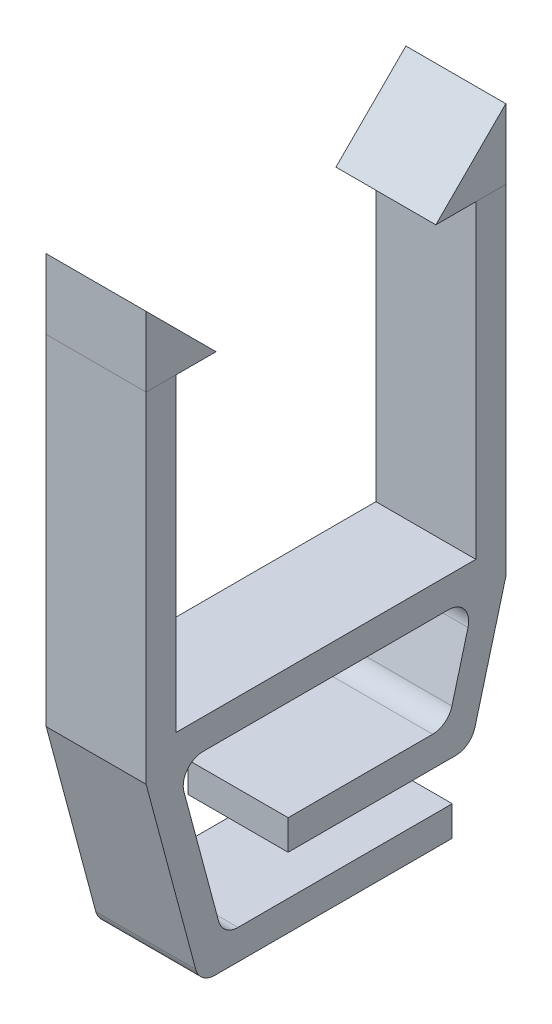
SolidWorks part; units mm, degrees
ref_plane "前视基准面" through (0, 0, 0) normal (0, 0, 1) x (1, 0, 0)
ref_plane "上视基准面" through (0, 0, 0) normal (0, 1, 0) x (1, 0, 0)
ref_plane "右视基准面" through (0, 0, 0) normal (1, 0, 0) x (0, 0, -1)
sketch "草图1" plane through (0, 0, 0) normal (0, 1, 0) x (1, 0, 0)
  line L1 (-10.9756, 9.0488) -> (-5.9756, 9.0488)
  line L2 (-10.9756, 9.0488) -> (-10.9756, -8.9512)
  line L3 (-10.9756, -8.9512) -> (-5.9756, -8.9512)
  line L4 (-5.9756, 9.0488) -> (-5.9756, -8.9512)
  line L5 (-10.9756, 7.5488) -> (-5.9756, 7.5488)
  line L6 (-10.9756, 7.5488) -> (-10.9756, -7.4512)
  line L7 (-10.9756, -7.4512) -> (-5.9756, -7.4512)
  line L8 (-5.9756, 7.5488) -> (-5.9756, -7.4512)
  dimension "D1" = 1.5
  dimension "D2" = 1.5
  dimension "D3" = 5
  dimension "D4" = 15
extrude "凸台-拉伸1" add sketch "草图1" along normal blind 15.5 contours L2 L5 L4 L1 | L7 L2 L3 L4
sketch "草图2" plane through (0, 0, 0) normal (0, -1, 0) x (1, 0, 0)
  line L1 (-5.9756, 8.9512) -> (-10.9756, 8.9512)
  line L2 (-5.9756, 8.9512) -> (-5.9756, -9.0488)
  line L3 (-5.9756, -9.0488) -> (-10.9756, -9.0488)
  line L4 (-10.9756, 8.9512) -> (-10.9756, -9.0488)
extrude "凸台-拉伸2" add sketch "草图2" along normal blind 1.5
sketch "草图3" plane through (-5.9756, 0, 0) normal (1, 0, 0) x (0, 0, -1)
  line L0 (9.0488, 15.5) -> (9.0488, 19)
  line L1 (9.0488, 19) -> (5.5488, 15.5)
  line L2 (5.5488, 15.5) -> (9.0488, 15.5)
  line L3 (-8.9512, 15.5) -> (-8.9512, 19)
  line L4 (-8.9512, 19) -> (-5.4512, 15.5)
  line L5 (-5.4512, 15.5) -> (-8.9512, 15.5)
  line L6 (-8.9512, -1.5) -> (-8.9512, 15.5) construction
  line L7 (-7.4512, 15.5) -> (-8.9512, 15.5) construction
  line L8 (9.0488, 15.5) -> (7.5488, 15.5) construction
  line L9 (9.0488, 15.5) -> (9.0488, -1.5) construction
  dimension "D1" = 3.5
  dimension "D2" = 3.5
  dimension "D3" = 3.5
  dimension "D4" = 3.5
extrude "凸台-拉伸3" add sketch "草图3" against normal blind 5 separate body
sketch "草图4" plane through (-5.9756, 0, 0) normal (1, 0, 0) x (0, 0, -1)
  line L0 (-8.9512, -1.5) -> (-6.2717, -11.5)
  line L1 (-6.2717, -11.5) -> (6.3693, -11.5)
  line L2 (6.3693, -11.5) -> (6.3693, -10)
  line L3 (6.3693, -10) -> (-5.1207, -10)
  line L4 (-5.1207, -10) -> (-7.3983, -1.5)
  line L5 (9.0488, -1.5) -> (-8.9512, -1.5) construction
  line L6 (-7.3983, -1.5) -> (-8.9512, -1.5)
  line L7 (9.0488, -1.5) -> (7.3071, -8)
  line L8 (7.3071, -8) -> (-1.8439, -8)
  line L9 (-1.8439, -8) -> (-1.8439, -6.5)
  line L10 (-1.8439, -6.5) -> (6.1561, -6.5)
  line L11 (6.1561, -6.5) -> (7.4959, -1.5)
  line L12 (7.4959, -1.5) -> (9.0488, -1.5)
  dimension "D1" = 1.5
  dimension "D2" = 1.5
  dimension "D3" = 1.5
  dimension "D4" = 1.5
  dimension "D5" = 5
  dimension "D6" = 2
  dimension "D7" = 8
  dimension "D8" = 75
  dimension "D9" = 75
extrude "凸台-拉伸4" add sketch "草图4" against normal blind 5
fillet "圆角1" radius 1 6 edges at (-8.4756, -11.5, 6.2717) (-8.4756, -10, 5.1207) (-8.4756, -8, -7.3071) (-8.4756, -6.5, -6.1561) (-8.4756, -1.5, 7.3983) (-8.4756, -1.5, -7.4959)
